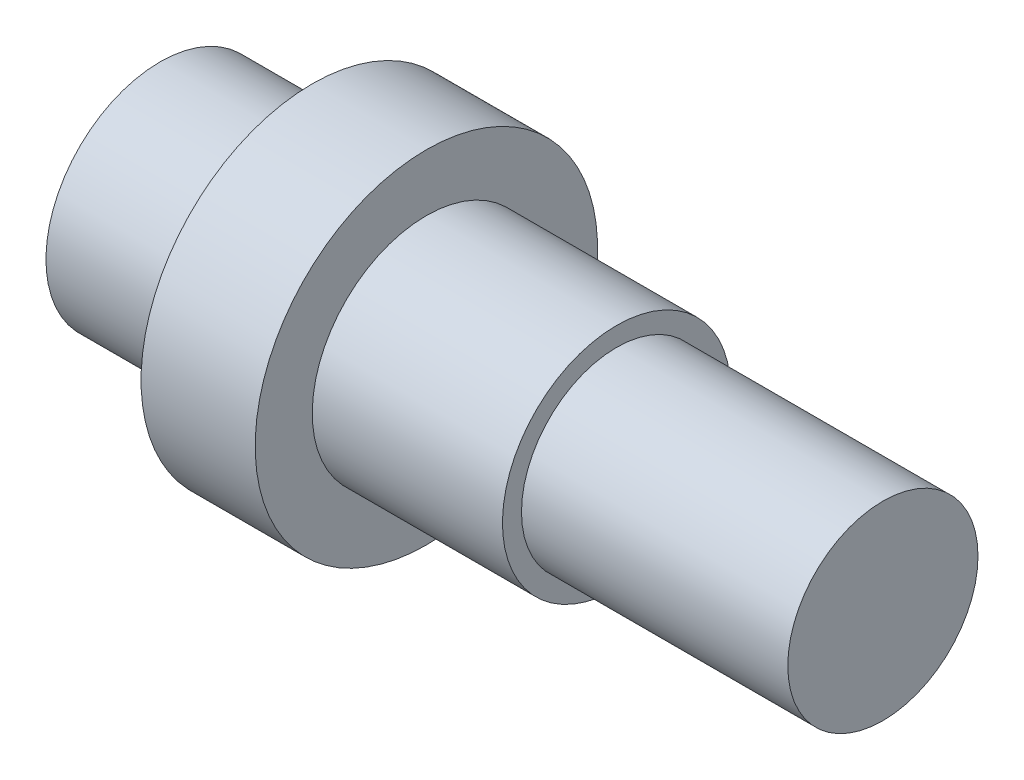
SolidWorks part; units mm, degrees
ref_plane "Přední rovina" through (0, 0, 0) normal (0, 0, 1) x (1, 0, 0)
ref_plane "Vrchní rovina" through (0, 0, 0) normal (0, 1, 0) x (1, 0, 0)
ref_plane "Pravá rovina" through (0, 0, 0) normal (1, 0, 0) x (0, 0, -1)
sketch "Skica1" plane through (0, 0, 0) normal (0, 0, 1) x (1, 0, 0)
  line L0 (0, 0) -> (0, 15)
  line L1 (0, 15) -> (20, 15)
  line L2 (20, 15) -> (20, 22.5)
  line L3 (20, 22.5) -> (35, 22.5)
  line L4 (35, 22.5) -> (35, 15)
  line L5 (35, 15) -> (60, 15)
  line L6 (60, 15) -> (60, 12.5)
  line L7 (60, 12.5) -> (95, 12.5)
  line L8 (95, 12.5) -> (95, 0)
  line L9 (95, 0) -> (0, 0) construction
  line L10 (0, 0) -> (95, 0)
  dimension "D1" = 30
  dimension "D2" = 45
  dimension "D3" = 25
  dimension "D4" = 20
  dimension "D5" = 15
  dimension "D6" = 25
  dimension "D7" = 35
revolve "Rotovat1" add sketch "Skica1" angle 360 about L9
